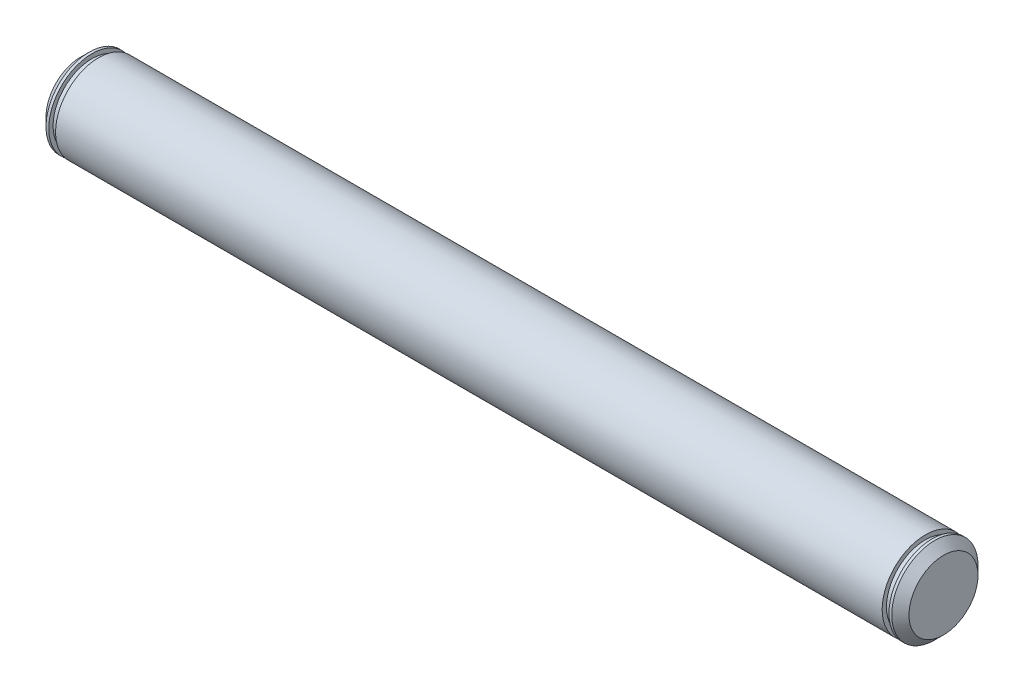
SolidWorks part; units mm, degrees
material "Plain Carbon Steel"
ref_plane "Front" through (0, 0, 0) normal (0, 0, 1) x (1, 0, 0)
ref_plane "Top" through (0, 0, 0) normal (0, 1, 0) x (1, 0, 0)
ref_plane "Right" through (0, 0, 0) normal (1, 0, 0) x (0, 0, -1)
sketch "Sketch1" plane through (0, 0, 0) normal (0, 0, 1) x (1, 0, 0)
  line L0 (-63.5, 0) -> (63.5, 0) construction
  line L1 (63.5, 6.35) -> (63.5, -6.35) construction
  line L2 (-63.5, 6.35) -> (-63.5, -6.35) construction
  dimension "Length" = 127
  dimension "Diameter" = 12.7
sketch "Sketch2" plane through (0, 0, 0) normal (1, 0, 0) x (0, 0, -1)
  circle A0 centre (0, 0) radius 6.35
extrude "Extrude1" add sketch "Sketch2" against normal up to vertex (63.5 mm away) and the other way up to vertex (63.5 mm away) up to point (-63.5, 6.35, 0) other way up to point (63.5, 6.35, 0)
chamfer "Chamfer1" distance 1.27 angle 45 2 edges at (63.5, 0, -6.35) (-63.5, 0, -6.35)
sketch "Sketch3" plane through (-60.3239, 0, 0) normal (-1, 0, 0) x (0, 0, 1)
  circle A0 centre (0, 0) radius 5.715
  circle A1 centre (0, 0) radius 6.35
  circle A2 centre (0, 0) radius 6.35 construction
  dimension "D1" = 11.43
extrude "Cut-Extrude1" cut sketch "Sketch3" along normal blind 1 from offset 0.5
mirror "Mirror1" about plane through (0, 0, 0) normal (1, 0, 0) of "Cut-Extrude1"
equation "\"D1@Chamfer1\" = \"Diameter@Sketch1\"*.1"
